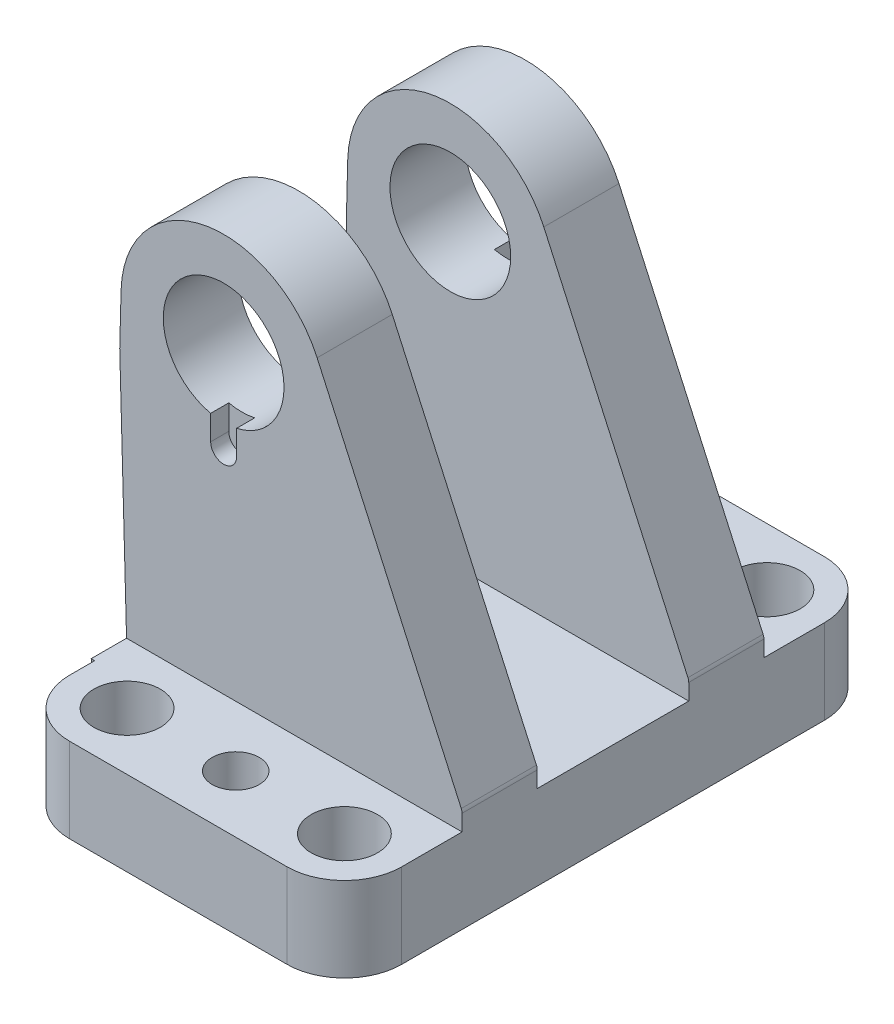
SolidWorks part; units mm, degrees
ref_plane "Front Plane" through (0, 0, 0) normal (0, 0, 1) x (1, 0, 0)
ref_plane "Top Plane" through (0, 0, 0) normal (0, 1, 0) x (1, 0, 0)
ref_plane "Right Plane" through (0, 0, 0) normal (1, 0, 0) x (0, 0, -1)
ref_plane "Plane1" through (0, 0, 0) normal (0, 1, 0) x (1, 0, 0)
sketch "Sketch1" plane through (0, 0, 0) normal (0, 1, 0) x (1, 0, 0)
  line L0 (-18, -44.5) -> (18, -44.5)
  line L1 (27.5, -35) -> (27.5, 35)
  line L2 (18, 44.5) -> (-18, 44.5)
  line L3 (-27.5, 35) -> (-27.5, -35)
  arc A0 (-27.5, -35) -> (-18, -44.5) centre (-18, -35) ccw
  arc A1 (18, -44.5) -> (27.5, -35) centre (18, -35) ccw
  arc A2 (27.5, 35) -> (18, 44.5) centre (18, 35) ccw
  arc A3 (-18, 44.5) -> (-27.5, 35) centre (-18, 35) ccw
  circle A4 centre (18, 35) radius 5.5
  circle A5 centre (18, -35) radius 5.5
  circle A6 centre (0, 35) radius 3.9
  circle A7 centre (0, -35) radius 3.9
  circle A8 centre (-18, 35) radius 5.5
  circle A9 centre (-18, -35) radius 5.5
extrude "Boss-Extrude1" add sketch "Sketch1" along normal blind 14
ref_plane "Plane2" through (0, 0, 0) normal (0, 0, 1) x (1, 0, 0)
sketch "Sketch2" plane through (0, 0, 0) normal (0, 0, 1) x (1, 0, 0)
  line L0 (-28.0857, 14) -> (-27.7, 0)
  line L1 (-27.7, 0) -> (-22.7, 0)
  line L2 (-22.7, 0) -> (-22.7, 14)
  line L3 (-22.7, 14) -> (-28.0857, 14)
extrude "Boss-Extrude2" add sketch "Sketch2" against normal blind 30.85 and the other way blind 30.85
ref_plane "Plane3" through (0, 0, 25) normal (0, 0, 1) x (1, 0, 0)
sketch "Sketch3" plane through (0, 0, 25) normal (0, 0, 1) x (1, 0, 0)
  line L0 (-29.2152, 55.003) -> (-27.7, 0)
  line L1 (-27.7, 0) -> (27.5, 0)
  line L2 (27.5, 0) -> (27.5, 16.6761)
  line L3 (27.3664, 17.295) -> (3.4853, 70.0146)
  line L4 (-28.9942, 63.445) -> (-29.2152, 55.003)
  arc A0 (27.5, 16.6761) -> (27.3664, 17.295) centre (26, 16.6761) ccw
  arc A1 (3.4853, 70.0146) -> (-28.9942, 63.445) centre (-12, 63) ccw
  circle A2 centre (-12, 63) radius 10
extrude "Boss-Extrude3" add sketch "Sketch3" against normal blind 12.45
ref_plane "Plane4" through (0, 0, -25) normal (0, 0, 1) x (1, 0, 0)
sketch "Sketch4" plane through (0, 0, -25) normal (0, 0, 1) x (1, 0, 0)
  line L0 (-29.2152, 55.003) -> (-27.7, 0)
  line L1 (-27.7, 0) -> (27.5, 0)
  line L2 (27.5, 0) -> (27.5, 16.6761)
  line L3 (27.3664, 17.295) -> (3.4853, 70.0146)
  line L4 (-28.9942, 63.445) -> (-29.2152, 55.003)
  arc A0 (27.5, 16.6761) -> (27.3664, 17.295) centre (26, 16.6761) ccw
  arc A1 (3.4853, 70.0146) -> (-28.9942, 63.445) centre (-12, 63) ccw
  circle A2 centre (-12, 63) radius 10
extrude "Boss-Extrude4" add sketch "Sketch4" along normal blind 12.45
ref_plane "Plane5" through (0, 0, 25) normal (0, 0, 1) x (1, 0, 0)
sketch "Sketch5" plane through (0, 0, 25) normal (0, 0, 1) x (1, 0, 0)
  line L0 (-9.85, 49.15) -> (-9.85, 63)
  line L1 (-9.85, 63) -> (-14.15, 63)
  line L2 (-14.15, 63) -> (-14.15, 49.15)
  arc A0 (-14.15, 49.15) -> (-9.85, 49.15) centre (-12, 49.15) ccw
extrude "Cut-Extrude1" cut sketch "Sketch5" against normal blind 3 and the other way blind 3
ref_plane "Plane6" through (0, 0, -25) normal (0, 0, 1) x (1, 0, 0)
sketch "Sketch6" plane through (0, 0, -25) normal (0, 0, 1) x (1, 0, 0)
  line L0 (-9.85, 49.15) -> (-9.85, 63)
  line L1 (-9.85, 63) -> (-14.15, 63)
  line L2 (-14.15, 63) -> (-14.15, 49.15)
  arc A0 (-14.15, 49.15) -> (-9.85, 49.15) centre (-12, 49.15) ccw
extrude "Cut-Extrude2" cut sketch "Sketch6" against normal blind 3 and the other way blind 3
